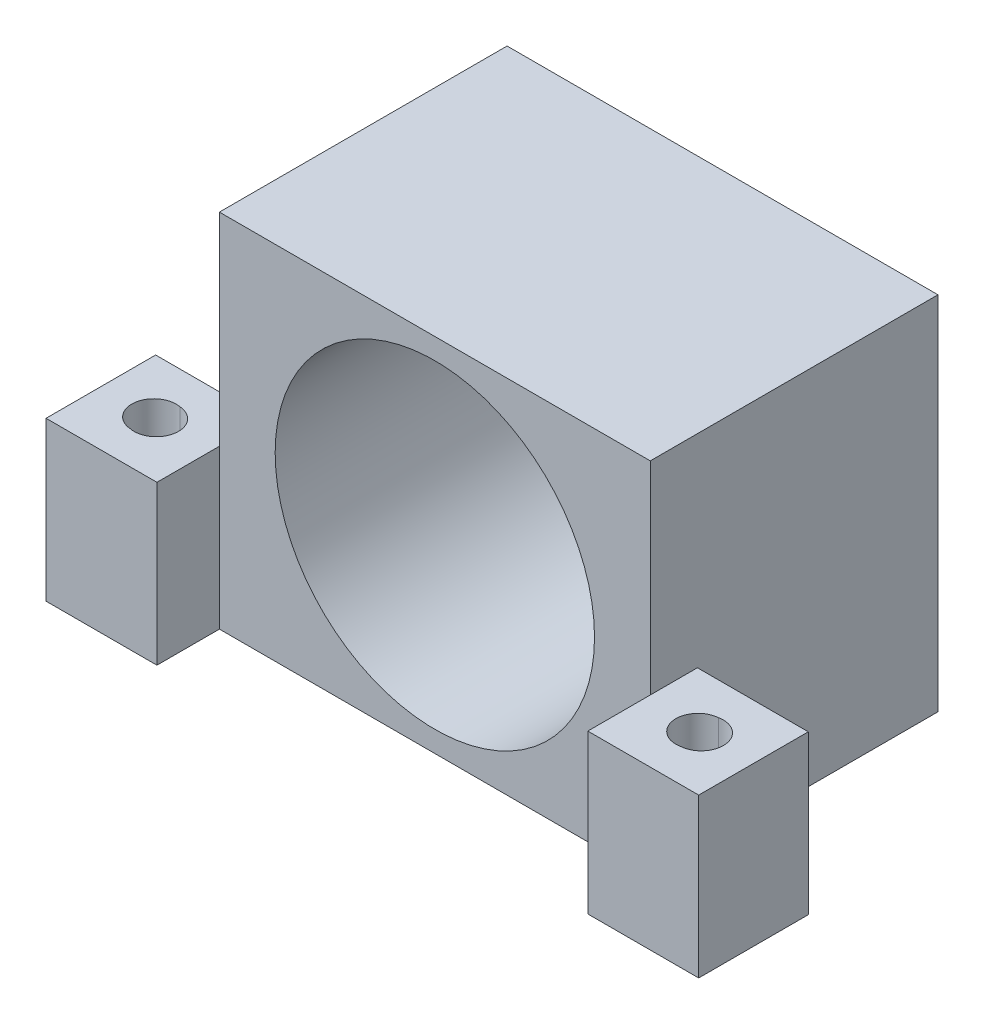
SolidWorks part; units mm, degrees
ref_plane "Front Plane" through (0, 0, 0) normal (0, 0, 1) x (1, 0, 0)
ref_plane "Top Plane" through (0, 0, 0) normal (0, 1, 0) x (1, 0, 0)
ref_plane "Right Plane" through (0, 0, 0) normal (1, 0, 0) x (0, 0, -1)
sketch "Sketch1" plane through (0, 0, 0) normal (0, 0, 1) x (1, 0, 0)
  line L0 (17, -14.25) -> (-17, -14.25)
  line L1 (-17, 14.25) -> (17, 14.25)
  line L2 (-17, 14.25) -> (-17, -14.25)
  line L3 (-17, 0) -> (17, 0) construction
  line L4 (17, 14.25) -> (17, -14.25)
  line L5 (0, 14.25) -> (0, -14.25) construction
  dimension "D2" = 34
  dimension "D3" = 28.5
extrude "Boss-Extrude1" add sketch "Sketch1" along normal blind 22.7
sketch "Sketch3" plane through (0, 0, 22.7) normal (0, 0, 1) x (1, 0, 0)
  circle A0 centre (0, 0) radius 12.6
  dimension "D1" = 25.2
extrude "Cut-Extrude1" cut sketch "Sketch3" against normal blind 21
sketch "Sketch5" plane through (0, 0, 1.7) normal (0, 0, 1) x (1, 0, 0)
  line L0 (13.102, 0) -> (-13.563, 0) construction
  line L1 (0, 12.3911) -> (0, -11.6995) construction
  line L2 (-11.4215, -11.4215) -> (11.4215, 11.4215) construction
  line L3 (10.5106, -10.5106) -> (-10.5106, 10.5106) construction
  circle A0 centre (6.0104, 6.0104) radius 1.625
  circle A1 centre (-6.0104, 6.0104) radius 1.625
  circle A2 centre (6.0104, -6.0104) radius 1.625
  circle A3 centre (-6.0104, -6.0104) radius 1.625
  circle A4 centre (0, 0) radius 8.5 construction
  circle A5 centre (0, 0) radius 3.75
  point P20 (0, 0)
  point P21 (0, 0)
  dimension "D1" = 3.25
  dimension "D2" = 17
  dimension "D3" = 7.5
  dimension "D4" = 45
  dimension "D5" = 45
extrude "Cut-Extrude2" cut sketch "Sketch5" against normal through all
sketch "Sketch7" plane through (0, 0, 22.7) normal (0, 0, 1) x (1, 0, 0)
  line L0 (0, 15.1888) -> (0, -15.3037) construction
  line L1 (-17, -1.75) -> (-25.75, -1.75)
  line L2 (-17, -1.75) -> (-17, -14.25)
  line L3 (-17, -14.25) -> (-25.75, -14.25)
  line L4 (-25.75, -1.75) -> (-25.75, -14.25)
  line L5 (17, -1.75) -> (25.75, -1.75)
  line L6 (17, -1.75) -> (17, -14.25)
  line L7 (17, -14.25) -> (25.75, -14.25)
  line L8 (25.75, -1.75) -> (25.75, -14.25)
  line L9 (17, -14.25) -> (17, 14.25) construction
  line L13 (-17, 14.25) -> (-17, -14.25) construction
  line L14 (-17, -14.25) -> (17, -14.25) construction
  dimension "D1" = 12.5
  dimension "D2" = 8.75
extrude "Boss-Extrude2" add sketch "Sketch7" along normal blind 4.93 and the other way blind 3.72
sketch "Sketch8" plane through (0, -1.75, 0) normal (0, 1, 0) x (1, 0, 0)
  line L0 (21.375, -27.63) -> (21.375, -18.98) construction
  line L1 (25.75, -27.63) -> (17, -27.63) construction
  line L2 (25.75, -18.98) -> (17, -18.98) construction
  line L3 (25.75, -23.305) -> (-25.75, -23.305) construction
  line L4 (25.75, -18.98) -> (25.75, -27.63) construction
  line L5 (-25.75, -18.98) -> (-25.75, -27.63) construction
  line L6 (0, 0) -> (0, -23.3809) construction
  circle A0 centre (21.375, -23.305) radius 1.75
  circle A1 centre (-21.375, -23.305) radius 1.75
  point P17 (21.375, -23.305)
  dimension "D1" = 3.5
extrude "Cut-Extrude3" cut sketch "Sketch8" against normal through all
sketch "Sketch9" plane through (0, -14.25, 0) normal (0, -1, 0) x (1, 0, 0)
  circle A0 centre (-21.375, 23.305) radius 3.25
  circle A1 centre (21.375, 23.305) radius 3.25
  dimension "D1" = 6.5
extrude "Cut-Extrude4" cut sketch "Sketch9" against normal blind 3.175
sketch "Sketch11" plane through (0, 0, 0) normal (0, 0, -1) x (-1, 0, 0)
  line L0 (-11.0405, 11.0405) -> (11.0405, -11.0405) construction
  line L1 (12.8573, 12.8573) -> (-12.8573, -12.8573) construction
  line L2 (-15.1803, 0) -> (19.6713, 0) construction
  line L3 (0, 16.5749) -> (0, -19.4111) construction
  circle A0 centre (-6.0104, 6.0104) radius 1.625 construction
  circle A1 centre (-6.0104, -6.0104) radius 1.625 construction
  circle A2 centre (6.0104, 6.0104) radius 1.625 construction
  circle A3 centre (6.0104, -6.0104) radius 1.625 construction
  circle A4 centre (0, 0) radius 8.5 construction
  circle A5 centre (0, 0) radius 3.75 construction
  circle A6 centre (6.0104, 6.0104) radius 2.8
  circle A7 centre (6.0104, -6.0104) radius 2.8
  circle A8 centre (-6.0104, -6.0104) radius 2.8
  circle A9 centre (-6.0104, 6.0104) radius 2.8
  point P24 (0, 0)
  point P25 (0, 0)
  dimension "D1" = 3.25
  dimension "D2" = 17
  dimension "D3" = 7.5
  dimension "D4" = 5.6
  dimension "D5" = 45
  dimension "D6" = 45
extrude "Cut-Extrude5" cut sketch "Sketch11" against normal blind 10 draft 45
extrude "Cut-Extrude6" cut sketch "Sketch12" against normal blind 50
sketch "Sketch12" plane through (132.274, 1.25, 24.7763) normal (0, 1, 0) x (1, 0, 0)
  line L1 (-149.324, -31.2437) -> (-115.324, -31.2437) construction
  line L4 (-132.559, -64.5637) -> (-132.559, 1.6963) construction
  circle A0 centre (-111.629, 2.4013) radius 1.651
  circle A1 centre (-111.629, -64.8887) radius 1.651
  circle A2 centre (-153.489, -64.8887) radius 1.651
  circle A3 centre (-153.489, 2.4013) radius 1.651
extrude "Cut-Extrude7" cut sketch "Sketch13" against normal blind 50
sketch "Sketch13" plane through (-132.274, 1.25, 87.2637) normal (0, 1, 0) x (-1, 0, 0)
  line L1 (-149.324, -31.3337) -> (-115.324, -31.3337) construction
  line L4 (-132.324, -65.6137) -> (-132.324, 1.6863) construction
  circle A0 centre (-110.734, 2.3213) radius 1.651
  circle A1 centre (-110.734, -64.9887) radius 1.651
  circle A2 centre (-153.914, -64.9887) radius 1.651
  circle A3 centre (-153.914, 2.3213) radius 1.651
extrude "Cut-Extrude8" cut sketch "Sketch14" against normal blind 50
sketch "Sketch14" plane through (132.324, 1.25, 25.7563) normal (0, 1, 0) x (1, 0, 0)
  line L1 (-149.324, -31.1737) -> (-115.324, -31.1737) construction
  line L4 (-132.324, -65.4037) -> (-132.324, 1.8463) construction
  circle A0 centre (-110.734, 2.4813) radius 1.75
  circle A1 centre (-110.734, -64.8287) radius 1.75
  circle A2 centre (-153.914, -64.8287) radius 1.75
  circle A3 centre (-153.914, 2.4813) radius 1.75
extrude "Cut-Extrude12" cut sketch "Sketch18" against normal blind 50
sketch "Sketch18" plane through (-132.324, 1.25, 88.1037) normal (0, 1, 0) x (-1, 0, 0)
  line L1 (-149.324, -31.1737) -> (-115.324, -31.1737) construction
  line L4 (-132.324, -65.4037) -> (-132.324, 1.8463) construction
  circle A0 centre (-110.734, 2.4813) radius 1.651
  circle A1 centre (-110.734, -64.8287) radius 1.651
  circle A2 centre (-153.914, -64.8287) radius 1.651
  circle A3 centre (-153.914, 2.4813) radius 1.651
